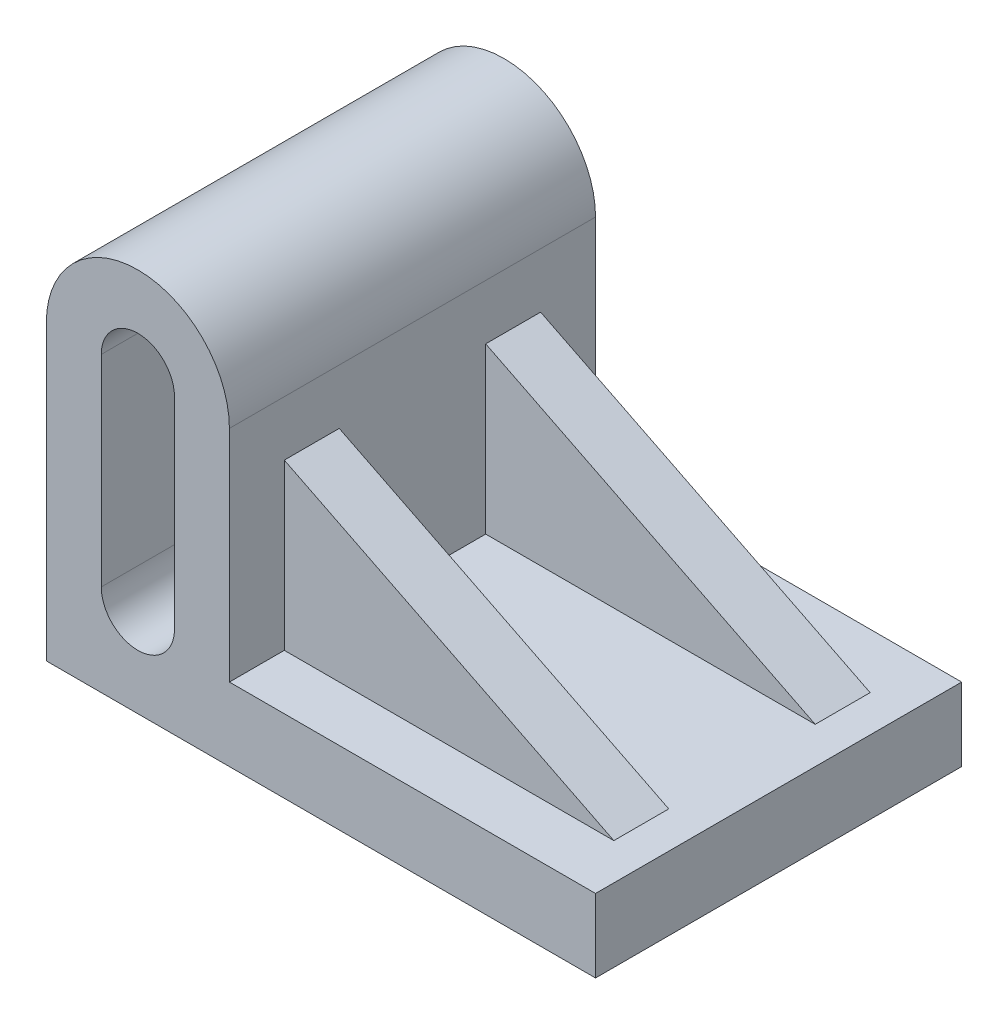
SolidWorks part; units mm, degrees
ref_plane "Front Plane" through (0, 0, 0) normal (0, 0, 1) x (1, 0, 0)
ref_plane "Top Plane" through (0, 0, 0) normal (0, 1, 0) x (1, 0, 0)
ref_plane "Right Plane" through (0, 0, 0) normal (1, 0, 0) x (0, 0, -1)
sketch "Sketch1" plane through (0, 0, 0) normal (0, 0, 1) x (1, 0, 0)
  line L0 (-50, 40) -> (-50, -15) construction
  line L1 (-75, 40) -> (75, 40)
  line L2 (-75, 40) -> (-75, -40)
  line L3 (-75, -40) -> (75, -40)
  line L4 (75, 40) -> (75, -40)
  line L5 (-75, 40) -> (75, -40) construction
  line L6 (-75, -40) -> (75, 40) construction
  line L7 (-40, 40) -> (-40, -15)
  line L8 (-60, 40) -> (-60, -15)
  line L9 (-25, 40) -> (-25, -40)
  line L10 (-25, -20) -> (75, -20)
  circle A0 centre (-50, 40) radius 25
  arc A1 (-40, 40) -> (-60, 40) centre (-50, 40) ccw
  arc A2 (-60, -15) -> (-40, -15) centre (-50, -15) ccw
  point P0 (0, 0)
  point P8 (-50, 12.5)
  dimension "D3" = 50
  dimension "D4" = 20
  dimension "D1" = 150
  dimension "D2" = 80
  dimension "D5" = 25
  dimension "D6" = 20
extrude "Boss-Extrude1" add sketch "Sketch1" along normal blind 100 contours L10 L9 L3 L4 | A2 L8 A0 L2 L3 L9 L7 | L7 A0 L1 | A1 L1 A0 | L1 A0 L8
sketch "Sketch2" plane through (0, -20, 0) normal (0, 1, 0) x (1, 0, 0)
  line L0 (-25, -100) -> (-25, 0) construction
  line L1 (-25, -15) -> (65, -15)
  line L2 (-25, -15) -> (-25, -85)
  line L3 (-25, -85) -> (65, -85)
  line L4 (65, -15) -> (65, -85)
  line L5 (75, -50) -> (53.383, -50) construction
  line L6 (75, -100) -> (75, 0) construction
  line L8 (-25, -30) -> (65, -30)
  line L9 (-25, -30) -> (-25, -70)
  line L10 (-25, -70) -> (65, -70)
  line L11 (65, -30) -> (65, -70)
  line M7 (-25, 0) -> (-25, -100)
  dimension "D1" = 10
  dimension "D2" = 70
  dimension "D3" = 15
extrude "Boss-Extrude2" add sketch "Sketch2" along normal blind 45 contours L10 L3 L4 M7 | L8 L4 L1 M7
sketch "Sketch3" plane through (0, 0, 85) normal (0, 0, 1) x (1, 0, 0)
  line L0 (-25, 25) -> (65, -20)
  line L5 (-25, -20) -> (65, -20)
  line L6 (65, -20) -> (65, 25)
  line L7 (65, 25) -> (-25, 25)
  line L8 (-25, 25) -> (-25, -20)
  line L9 (-25, -20) -> (65, -20)
  line L10 (65, -20) -> (65, 25)
  line L11 (65, 25) -> (-25, 25)
  line L12 (-25, 25) -> (-25, -20)
  line M6 (65, -20) -> (65, 25)
  line M7 (65, 25) -> (-25, 25)
  dimension "D1" = 0
extrude "Cut-Extrude1" cut sketch "Sketch3" against normal through all contours L0 M7 M6
